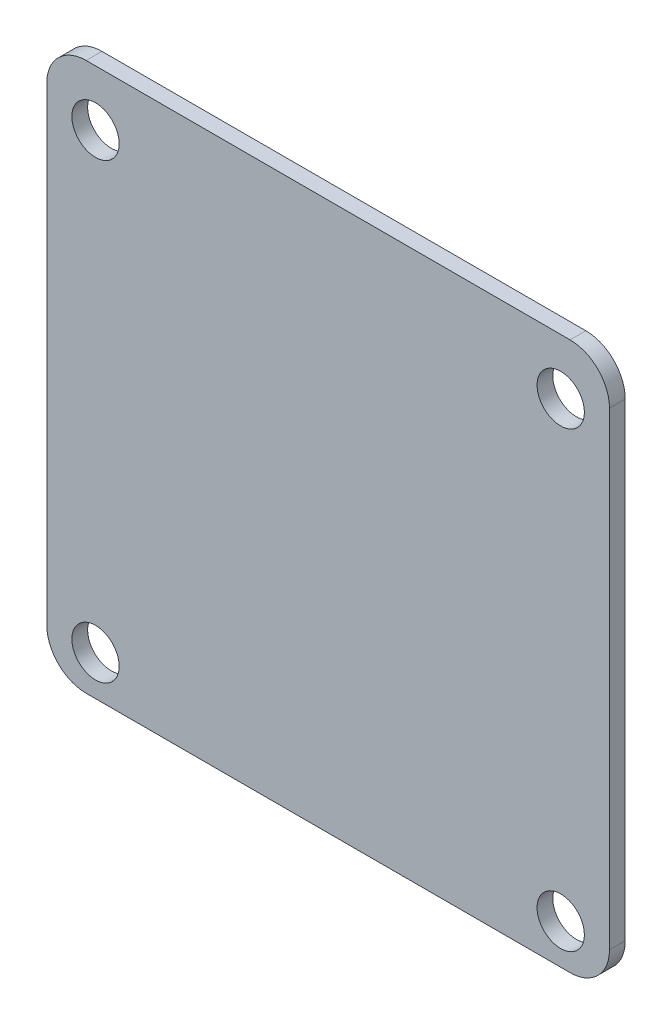
SolidWorks part; units mm, degrees
material "Verre"
ref_plane "Plan de face" through (0, 0, 0) normal (0, 0, 1) x (1, 0, 0)
ref_plane "Plan de dessus" through (0, 0, 0) normal (0, 1, 0) x (1, 0, 0)
ref_plane "Plan de droite" through (0, 0, 0) normal (1, 0, 0) x (0, 0, -1)
sketch "Esquisse1" plane through (0, 0, 0) normal (0, 0, 1) x (1, 0, 0)
  line L0 (113.1013, -62.0246) -> (143.7871, -62.0246)
  line L1 (146.2871, -64.5246) -> (146.2871, -94.2784)
  line L2 (143.7871, -96.7784) -> (113.1013, -96.7784)
  line L3 (110.6013, -64.5246) -> (110.6013, -94.2784)
  arc A0 (110.6013, -94.2784) -> (113.1013, -96.7784) centre (113.1013, -94.2784) ccw
  arc A1 (113.1013, -62.0246) -> (110.6013, -64.5246) centre (113.1013, -64.5246) ccw
  arc A2 (143.7871, -62.0246) -> (146.2871, -64.5246) centre (143.7871, -64.5246) cw
  circle A3 centre (143.1942, -65.5515) radius 1.5
  circle A4 centre (113.6942, -65.5515) radius 1.5
  circle A5 centre (113.6942, -94.2515) radius 1.5
  circle A6 centre (143.1942, -94.2515) radius 1.5
  arc A7 (143.7871, -96.7784) -> (146.2871, -94.2784) centre (143.7871, -94.2784) ccw
extrude "Boss.-Extru.1" add sketch "Esquisse1" along normal blind 1
